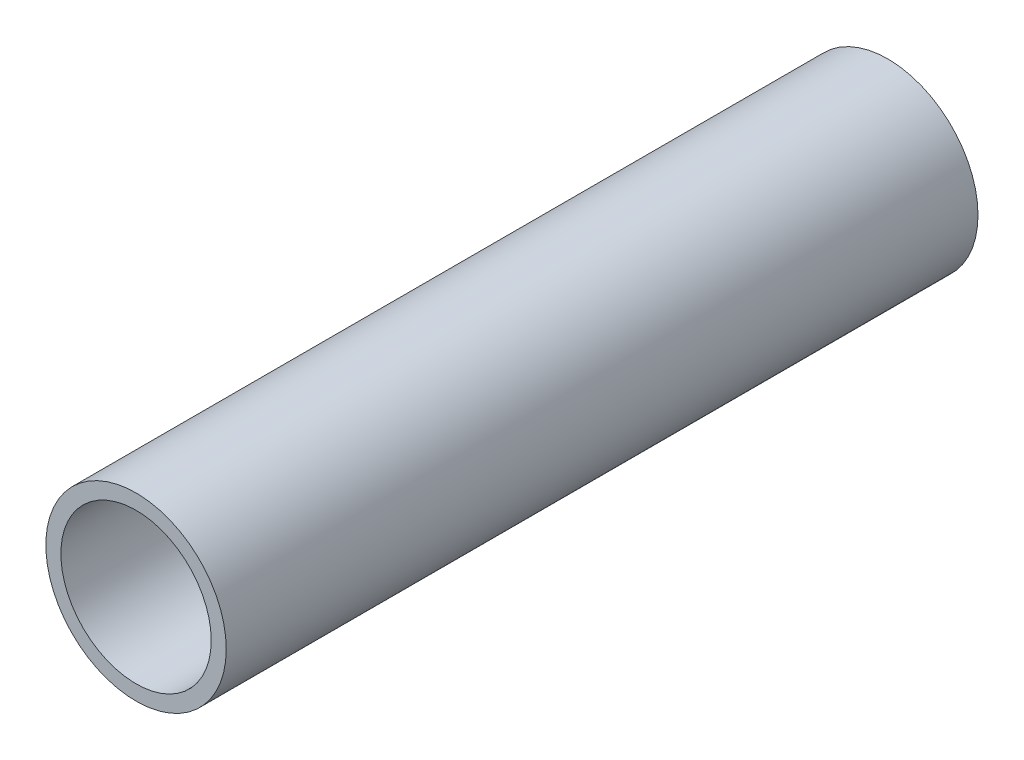
SolidWorks part; units mm, degrees
ref_plane "Front" through (0, 0, 0) normal (0, 0, 1) x (1, 0, 0)
ref_plane "Top" through (0, 0, 0) normal (0, 1, 0) x (1, 0, 0)
ref_plane "Right" through (0, 0, 0) normal (1, 0, 0) x (0, 0, -1)
sketch "Эскиз1" plane through (0, 0, 0) normal (0, 0, 1) x (1, 0, 0)
  circle A0 centre (0, 0) radius 50
  circle A1 centre (0, 0) radius 60
  dimension "D1" = 120
  dimension "D2" = 100
extrude "Бобышка-Вытянуть1" add sketch "Эскиз1" along normal blind 500
